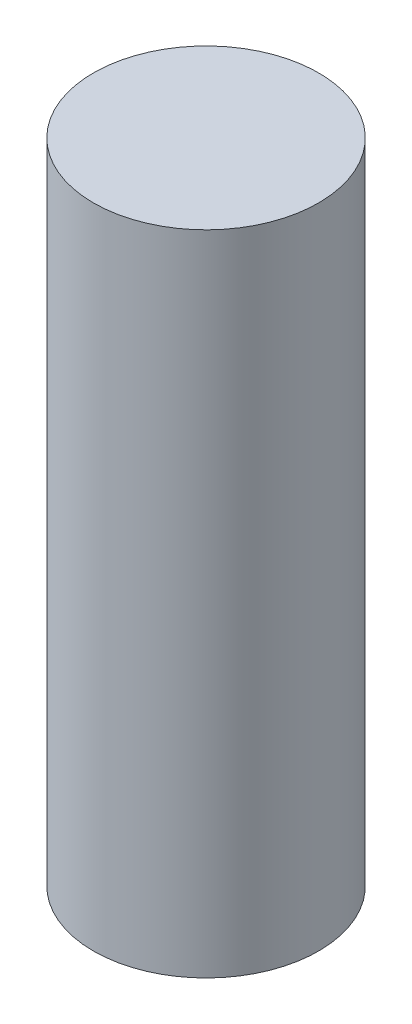
SolidWorks part; units mm, degrees
ref_plane "Front Plane" through (0, 0, 0) normal (0, 0, 1) x (1, 0, 0)
ref_plane "Top Plane" through (0, 0, 0) normal (0, 1, 0) x (1, 0, 0)
ref_plane "Right Plane" through (0, 0, 0) normal (1, 0, 0) x (0, 0, -1)
sketch "Sketch1" plane through (0, 0, 0) normal (0, 1, 0) x (1, 0, 0)
  line L0 (0, 0) -> (-109.2351, -37.0849) construction
  circle A0 centre (0, 45.445) radius 1.925
extrude "Boss-Extrude1" add sketch "Sketch1" along normal blind 11.0744
